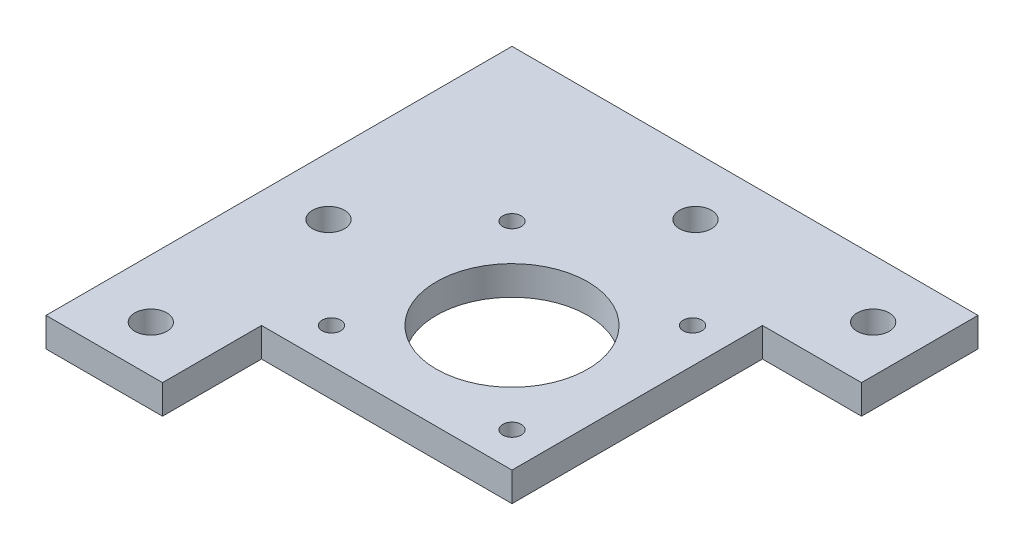
SolidWorks part; units mm, degrees
ref_plane "Front Plane" through (0, 0, 0) normal (0, 0, 1) x (1, 0, 0)
ref_plane "Top Plane" through (0, 0, 0) normal (0, 1, 0) x (1, 0, 0)
ref_plane "Right Plane" through (0, 0, 0) normal (1, 0, 0) x (0, 0, -1)
sketch "Sketch2" plane through (0, 0, 0) normal (0, 1, 0) x (1, 0, 0)
  line L0 (0, 0) -> (20, 0)
  line L1 (20, 0) -> (20, 17)
  line L2 (20, 17) -> (63, 17)
  line L3 (63, 17) -> (63, 60)
  line L4 (63, 60) -> (80, 60)
  line L5 (80, 60) -> (80, 80)
  line L6 (80, 80) -> (0, 80)
  line L7 (0, 80) -> (0, 0)
  line L8 (26, 54) -> (57, 23) construction
  line L9 (26, 23) -> (57, 54) construction
  circle A0 centre (57, 23) radius 1.6
  circle A1 centre (57, 54) radius 1.6
  circle A2 centre (26, 23) radius 1.6
  circle A3 centre (26, 54) radius 1.6
  circle A4 centre (41.5, 38.5) radius 13
  circle A5 centre (10, 8) radius 2.75
  circle A7 centre (72, 70) radius 2.75
  circle A8 centre (41.5, 70) radius 2.75
  circle A9 centre (10, 38.5) radius 2.75
  point P27 (10, 54)
  point P28 (0, 0)
  point P29 (0, 0)
  point P30 (0, 0)
  dimension "D4" = 3.2
  dimension "D9" = 26
  dimension "D10" = 5.5
  dimension "D1" = 20
  dimension "D2" = 43
  dimension "D3" = 80
  dimension "D5" = 31
  dimension "D6" = 31
  dimension "D7" = 6
  dimension "D8" = 6
  dimension "D11" = 10
  dimension "D12" = 10
  dimension "D13" = 8
  dimension "D14" = 8
extrude "Boss-Extrude1" add sketch "Sketch2" along normal blind 5
